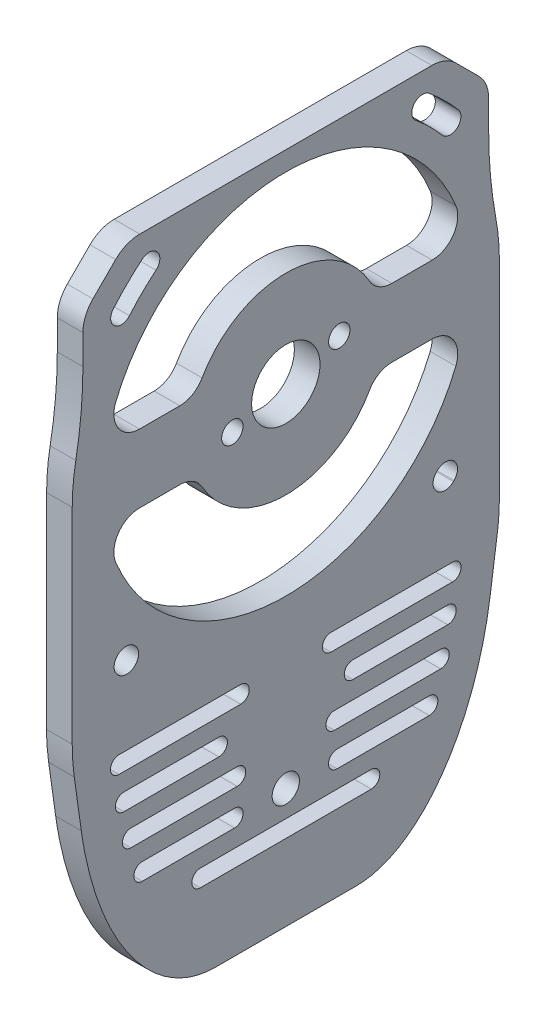
SolidWorks part; units mm, degrees
material "Thornel Mat VMA"
ref_plane "Front Plane" through (0, 0, 0) normal (0, 0, 1) x (1, 0, 0)
ref_plane "Top Plane" through (0, 0, 0) normal (0, 1, 0) x (1, 0, 0)
ref_plane "Right Plane" through (0, 0, 0) normal (1, 0, 0) x (0, 0, -1)
sketch "Sketch2" plane through (-80.1, 0, 0) normal (-1, 0, 0) x (0, 0, 1)
  line L0 (-10.1242, 29.75) -> (10.1242, 29.75)
  line L15 (23.9369, -27.3245) -> (24.7602, -21.4587)
  line L16 (25, -18.0135) -> (25, 6)
  line L17 (23.75, 19.6359) -> (23.75, 23.0931)
  line L18 (22.5784, 25.9216) -> (19.9216, 28.5784)
  line L19 (17.0931, 29.75) -> (10.1242, 29.75)
  line L20 (5.7689, 32.98) -> (1, 32.98)
  line L21 (1, 32.98) -> (1, 27.4767)
  line L22 (-1, 27.4767) -> (-1, 32.98)
  line L23 (-1, 32.98) -> (-5.7689, 32.98)
  line L24 (-10.1242, 29.75) -> (-17.0931, 29.75)
  line L25 (-19.9216, 28.5784) -> (-22.5784, 25.9216)
  line L26 (-23.75, 23.0931) -> (-23.75, 19.6359)
  line L27 (-25, 6) -> (-25, -18.0135)
  line L28 (-24.7602, -21.4587) -> (-23.9369, -27.3245)
  line L29 (-8.2627, -49) -> (8.2627, -49)
  line L30 (23.9369, -27.3245) -> (24.7602, -21.4587)
  line L31 (25, -18.0135) -> (25, 6)
  line L32 (23.75, 19.6359) -> (23.75, 23.0931)
  line L33 (22.5784, 25.9216) -> (19.9216, 28.5784)
  line L34 (17.0931, 29.75) -> (10.1242, 29.75)
  line L35 (5.7689, 32.98) -> (1, 32.98)
  line L36 (1, 32.98) -> (1, 27.4767)
  line L37 (-1, 27.4767) -> (-1, 32.98)
  line L38 (-1, 32.98) -> (-5.7689, 32.98)
  line L39 (-10.1242, 29.75) -> (-17.0931, 29.75)
  line L40 (-19.9216, 28.5784) -> (-22.5784, 25.9216)
  line L41 (-23.75, 23.0931) -> (-23.75, 19.6359)
  line L42 (-25, 6) -> (-25, -18.0135)
  line L43 (-24.7602, -21.4587) -> (-23.9369, -27.3245)
  line L44 (-8.2627, -49) -> (8.2627, -49)
  circle A0 centre (0, 6) radius 21.5
  arc A13 (25, 6) -> (24.5833, 10.5453) centre (0, 6) ccw
  arc A14 (23.75, 19.6359) -> (24.5833, 10.5453) centre (73.75, 19.6359) ccw
  arc A15 (23.75, 23.0931) -> (22.5784, 25.9216) centre (19.75, 23.0931) ccw
  arc A16 (19.9216, 28.5784) -> (17.0931, 29.75) centre (17.0931, 25.75) ccw
  arc A17 (7.207, 31.0132) -> (10.1242, 29.75) centre (10.1242, 33.75) ccw
  arc A18 (5.7689, 32.98) -> (7.207, 31.0132) centre (14.5, 37.8551) ccw
  arc A19 (-1, 27.4767) -> (1, 27.4767) centre (0, 6) ccw
  arc A20 (-7.207, 31.0132) -> (-5.7689, 32.98) centre (-14.5, 37.8551) ccw
  arc A21 (-10.1242, 29.75) -> (-7.207, 31.0132) centre (-10.1242, 33.75) ccw
  arc A22 (-17.0931, 29.75) -> (-19.9216, 28.5784) centre (-17.0931, 25.75) ccw
  arc A23 (-22.5784, 25.9216) -> (-23.75, 23.0931) centre (-19.75, 23.0931) ccw
  arc A24 (-24.5833, 10.5453) -> (-23.75, 19.6359) centre (-73.75, 19.6359) ccw
  arc A25 (-24.5833, 10.5453) -> (-25, 6) centre (0, 6) ccw
  arc A26 (25, 6) -> (24.5833, 10.5453) centre (0, 6) ccw
  arc A27 (23.75, 19.6359) -> (24.5833, 10.5453) centre (73.75, 19.6359) ccw
  arc A28 (23.75, 23.0931) -> (22.5784, 25.9216) centre (19.75, 23.0931) ccw
  arc A29 (19.9216, 28.5784) -> (17.0931, 29.75) centre (17.0931, 25.75) ccw
  arc A30 (7.207, 31.0132) -> (10.1242, 29.75) centre (10.1242, 33.75) ccw
  arc A31 (5.7689, 32.98) -> (7.207, 31.0132) centre (14.5, 37.8551) ccw
  arc A32 (-1, 27.4767) -> (1, 27.4767) centre (0, 6) ccw
  arc A33 (-7.207, 31.0132) -> (-5.7689, 32.98) centre (-14.5, 37.8551) ccw
  arc A34 (-10.1242, 29.75) -> (-7.207, 31.0132) centre (-10.1242, 33.75) ccw
  arc A35 (-17.0931, 29.75) -> (-19.9216, 28.5784) centre (-17.0931, 25.75) ccw
  arc A36 (-22.5784, 25.9216) -> (-23.75, 23.0931) centre (-19.75, 23.0931) ccw
  arc A37 (-24.5833, 10.5453) -> (-23.75, 19.6359) centre (-73.75, 19.6359) ccw
  arc A38 (-24.5833, 10.5453) -> (-25, 6) centre (0, 6) ccw
  ellipse E4 centre (10, -18.0135) end of major axis (10, -37.3575) minor radius 15 (24.7602, -21.4587) -> (25, -18.0135) ccw
  ellipse E5 centre (-10, -18.0135) end of major axis (-10, -37.3575) minor radius 15 (-25, -18.0135) -> (-24.7602, -21.4587) ccw
  ellipse E6 centre (-9.3222, -22.8431) end of major axis (-10.8998, 3.2982) minor radius 15 (-23.9369, -27.3245) -> (-8.2627, -49) ccw
  ellipse E7 centre (9.3222, -22.8431) end of major axis (7.7445, -48.9844) minor radius 15 (8.2627, -49) -> (23.9369, -27.3245) ccw
  ellipse E8 centre (10, -18.0135) end of major axis (10, -37.3575) minor radius 15 (24.7602, -21.4587) -> (25, -18.0135) ccw
  ellipse E9 centre (-10, -18.0135) end of major axis (-10, -37.3575) minor radius 15 (-25, -18.0135) -> (-24.7602, -21.4587) ccw
  ellipse E10 centre (-9.3222, -22.8431) end of major axis (-7.7445, -48.9844) minor radius 15 (-23.9369, -27.3245) -> (-8.2627, -49) ccw
  ellipse E11 centre (9.3222, -22.8431) end of major axis (7.7445, -48.9844) minor radius 15 (8.2627, -49) -> (23.9369, -27.3245) ccw
  dimension "D1" = 0
extrude "Boss-Extrude1" add sketch "Sketch2" along normal blind 3 contours L44 E11 L30 E8 L31 A26 A27 L32 A28 L33 A29 L34 L0 L36 A0 L37 L39 A35 L40 A36 L41 A37 A38 L42 E9 L43 E10 | A0 L36 L0 L37
sketch "Sketch3" plane through (-83.1, 0, 0) normal (-1, 0, 0) x (0, 0, 1)
  line L0 (0, 29.75) -> (0, -49) construction
  line L1 (17.0931, 29.75) -> (-17.0931, 29.75) construction
  line L2 (-8.2627, -49) -> (8.2627, -49) construction
  line L3 (-23.75, 23.0931) -> (-23.75, 19.6359) construction
  line L5 (18.3358, -17.75) -> (8.8925, -17.75)
  line L6 (19.2977, -17.2023) -> (19.0429, -17.4571)
  line L8 (18.3931, -19.4571) -> (19.8073, -18.0429)
  line L9 (8.8925, -19.75) -> (17.686, -19.75)
  line L10 (18.3358, -17.75) -> (8.8925, -17.75)
  line L11 (19.2977, -17.2023) -> (19.0429, -17.4571)
  line L13 (18.3931, -19.4571) -> (19.8073, -18.0429)
  line L14 (8.8925, -19.75) -> (17.686, -19.75)
  line L15 (-19.0429, -17.4571) -> (-19.2977, -17.2023)
  line L16 (-19.0429, -17.4571) -> (-19.2977, -17.2023)
  line L18 (-8.8925, -17.75) -> (-18.3358, -17.75)
  line L35 (-8.8925, -17.75) -> (-18.3358, -17.75)
  line L36 (-17.686, -19.75) -> (-8.8925, -19.75)
  line L37 (-17.686, -19.75) -> (-8.8925, -19.75)
  line L38 (-19.8073, -18.0429) -> (-18.3931, -19.4571)
  line L39 (-19.8073, -18.0429) -> (-18.3931, -19.4571)
  arc A4 (17.6468, -11.7085) -> (17.7085, -11.6468) centre (0, 6) ccw
  arc A5 (19.6918, -13.6232) -> (17.7085, -11.6468) centre (18.7002, -12.635) ccw
  arc A6 (19.6232, -13.6918) -> (19.6918, -13.6232) centre (0, 6) ccw
  arc A7 (17.6468, -11.7085) -> (19.6232, -13.6918) centre (18.635, -12.7002) ccw
  arc A8 (17.6468, -11.7085) -> (17.7085, -11.6468) centre (0, 6) ccw
  arc A9 (19.6918, -13.6232) -> (17.7085, -11.6468) centre (18.7002, -12.635) ccw
  arc A10 (19.6232, -13.6918) -> (19.6918, -13.6232) centre (0, 6) ccw
  arc A11 (17.6468, -11.7085) -> (19.6232, -13.6918) centre (18.635, -12.7002) ccw
  arc A16 (16.7926, 27.0708) -> (15.1966, 25.1465) centre (15.9946, 26.1087) ccw
  arc A17 (20.203, 23.6988) -> (16.7926, 27.0708) centre (-0.7636, 5.904) ccw
  arc A18 (18.297, 22.081) -> (20.203, 23.6988) centre (19.25, 22.8899) ccw
  arc A19 (18.297, 22.081) -> (15.1966, 25.1465) centre (-0.7636, 5.904) ccw
  arc A24 (-15.1966, 25.1465) -> (-16.7926, 27.0708) centre (-15.9946, 26.1087) ccw
  arc A25 (-15.1966, 25.1465) -> (-18.297, 22.081) centre (0.7636, 5.904) ccw
  arc A26 (-20.203, 23.6988) -> (-18.297, 22.081) centre (-19.25, 22.8899) ccw
  arc A27 (-16.7926, 27.0708) -> (-20.203, 23.6988) centre (0.7636, 5.904) ccw
  arc A28 (-19.6918, -13.6232) -> (-19.6232, -13.6918) centre (0, 6) ccw
  arc A29 (-17.7085, -11.6468) -> (-19.6918, -13.6232) centre (-18.7002, -12.635) ccw
  arc A30 (-17.7085, -11.6468) -> (-17.6468, -11.7085) centre (0, 6) ccw
  arc A31 (-19.6232, -13.6918) -> (-17.6468, -11.7085) centre (-18.635, -12.7002) ccw
  arc A32 (-19.6918, -13.6232) -> (-19.6232, -13.6918) centre (0, 6) ccw
  arc A33 (-17.7085, -11.6468) -> (-19.6918, -13.6232) centre (-18.7002, -12.635) ccw
  arc A34 (-17.7085, -11.6468) -> (-17.6468, -11.7085) centre (0, 6) ccw
  arc A35 (-19.6232, -13.6918) -> (-17.6468, -11.7085) centre (-18.635, -12.7002) ccw
  arc A38 (18.3358, -17.75) -> (19.0429, -17.4571) centre (18.3358, -16.75) ccw
  arc A39 (20.1002, -17.3358) -> (19.2977, -17.2023) centre (19.6512, -17.5559) ccw
  arc A40 (19.8073, -18.0429) -> (20.1002, -17.3358) centre (19.1002, -17.3358) ccw
  arc A41 (17.686, -19.75) -> (18.3931, -19.4571) centre (17.686, -18.75) ccw
  arc A42 (7.9787, -18.3437) -> (8.8925, -19.75) centre (8.8925, -18.75) ccw
  arc A43 (8.8925, -17.75) -> (7.9787, -18.3437) centre (8.8925, -18.75) ccw
  arc A44 (18.3358, -17.75) -> (19.0429, -17.4571) centre (18.3358, -16.75) ccw
  arc A45 (20.1002, -17.3358) -> (19.2977, -17.2023) centre (19.6512, -17.5559) ccw
  arc A46 (19.8073, -18.0429) -> (20.1002, -17.3358) centre (19.1002, -17.3358) ccw
  arc A47 (17.686, -19.75) -> (18.3931, -19.4571) centre (17.686, -18.75) ccw
  arc A48 (7.9787, -18.3437) -> (8.8925, -19.75) centre (8.8925, -18.75) ccw
  arc A49 (8.8925, -17.75) -> (7.9787, -18.3437) centre (8.8925, -18.75) ccw
  arc A50 (-19.2977, -17.2023) -> (-20.1002, -17.3358) centre (-19.6512, -17.5559) ccw
  arc A52 (-19.2977, -17.2023) -> (-20.1002, -17.3358) centre (-19.6512, -17.5559) ccw
  arc A54 (-19.0429, -17.4571) -> (-18.3358, -17.75) centre (-18.3358, -16.75) ccw
  arc A67 (-19.0429, -17.4571) -> (-18.3358, -17.75) centre (-18.3358, -16.75) ccw
  arc A69 (-7.9787, -18.3437) -> (-8.8925, -17.75) centre (-8.8925, -18.75) ccw
  arc A71 (-7.9787, -18.3437) -> (-8.8925, -17.75) centre (-8.8925, -18.75) ccw
  arc A73 (-8.8925, -19.75) -> (-7.9787, -18.3437) centre (-8.8925, -18.75) ccw
  arc A75 (-8.8925, -19.75) -> (-7.9787, -18.3437) centre (-8.8925, -18.75) ccw
  arc A77 (-18.3931, -19.4571) -> (-17.686, -19.75) centre (-17.686, -18.75) ccw
  arc A79 (-18.3931, -19.4571) -> (-17.686, -19.75) centre (-17.686, -18.75) ccw
  arc A81 (-20.1002, -17.3358) -> (-19.8073, -18.0429) centre (-19.1002, -17.3358) ccw
  arc A83 (-20.1002, -17.3358) -> (-19.8073, -18.0429) centre (-19.1002, -17.3358) ccw
  dimension "D2" = 1.25
  dimension "D7" = 3.2554
  dimension "D10" = 25
  dimension "D3" = 3.2188
  dimension "D8" = 3.6413
  dimension "D9" = 4.5
  dimension "D1" = 0
  dimension "D4" = 0
  dimension "D5" = 0
  dimension "D6" = 0
extrude "Cut-Extrude1" cut sketch "Sketch3" against normal through all contours A24 A27 A26 A25 | A32 A35 A34 A33 | A8 A11 A10 A9 | A19 A18 A17 A16
sketch "Sketch4" plane through (-80.1, 0, 0) normal (1, 0, 0) x (0, 0, -1)
  circle A0 centre (0, -35) radius 1.6
  dimension "D1" = 3.2
  dimension "D2" = 35
extrude "Cut-Extrude2" cut sketch "Sketch4" against normal through all contours A0
sketch "Sketch5" plane through (-80.1, 0, 0) normal (1, 0, 0) x (0, 0, -1)
  line L0 (-19.5212, -22.8125) -> (-5.2845, -22.8125) construction
  line L3 (-19.5212, -21.8125) -> (-5.2845, -21.8125)
  line L16 (0, -15.5) -> (0, -49) construction
  line L17 (8.2627, -49) -> (-8.2627, -49) construction
  line L18 (-19.5212, -23.8125) -> (-5.2845, -23.8125)
  line L19 (-18.9502, -26.875) -> (-7.8381, -26.875) construction
  line L20 (-18.9502, -25.875) -> (-7.8381, -25.875)
  line L21 (-18.9502, -27.875) -> (-7.8381, -27.875)
  line L22 (-16.7931, -35) -> (-6, -35) construction
  line L23 (-16.7931, -34) -> (-6, -34)
  line L24 (-16.7931, -36) -> (-6, -36)
  line L25 (-10, -39.0625) -> (10, -39.0625) construction
  line L26 (-8.2627, -45) -> (8.2627, -45)
  line L27 (19.9757, -26.7686) -> (20.799, -20.9028)
  line L28 (21, -18.0135) -> (21, 6)
  line L29 (19.75, 19.6359) -> (19.75, 23.0931)
  line L30 (19.75, 23.0931) -> (17.0931, 25.75)
  line L31 (17.0931, 25.75) -> (-17.0931, 25.75)
  line L32 (-17.0931, 25.75) -> (-19.75, 23.0931)
  line L33 (-19.75, 23.0931) -> (-19.75, 19.6359)
  line L34 (-21, 6) -> (-21, -18.0135)
  line L35 (-20.799, -20.9028) -> (-19.9757, -26.7686)
  line L36 (-8.2627, -45) -> (8.2627, -45) construction
  line L37 (19.9757, -26.7686) -> (20.799, -20.9028) construction
  line L38 (21, -18.0135) -> (21, 6) construction
  line L39 (19.75, 19.6359) -> (19.75, 23.0931) construction
  line L40 (19.75, 23.0931) -> (17.0931, 25.75) construction
  line L41 (17.0931, 25.75) -> (-17.0931, 25.75) construction
  line L42 (-17.0931, 25.75) -> (-19.75, 23.0931) construction
  line L43 (-19.75, 23.0931) -> (-19.75, 19.6359) construction
  line L44 (-21, 6) -> (-21, -18.0135) construction
  line L45 (-20.799, -20.9028) -> (-19.9757, -26.7686) construction
  line L46 (-10, -38.0625) -> (10, -38.0625)
  line L47 (-10, -40.0625) -> (10, -40.0625)
  line L48 (-18.13, -30.9375) -> (-5.6903, -30.9375) construction
  line L49 (-8.3434, -18.75) -> (-8.3434, -22.8125) construction
  line L50 (-8.3434, -22.8125) -> (-8.3434, -26.875) construction
  line L51 (-18.13, -29.9375) -> (-5.6903, -29.9375)
  line L52 (-6, -35) -> (-6, -39.0625) construction
  line L53 (19.5212, -22.8125) -> (5.2845, -22.8125) construction
  line L54 (19.5212, -21.8125) -> (5.2845, -21.8125)
  line L55 (19.5212, -23.8125) -> (5.2845, -23.8125)
  line L56 (18.9502, -26.875) -> (7.8381, -26.875) construction
  line L57 (18.9502, -25.875) -> (7.8381, -25.875)
  line L58 (18.9502, -27.875) -> (7.8381, -27.875)
  line L59 (16.7931, -35) -> (6, -35) construction
  line L60 (16.7931, -34) -> (6, -34)
  line L61 (16.7931, -36) -> (6, -36)
  line L62 (-18.13, -31.9375) -> (-5.6903, -31.9375)
  line L63 (-8.3434, -26.875) -> (-8.3434, -30.9375) construction
  line L64 (-8.3434, -30.9375) -> (-8.3434, -35) construction
  line L65 (18.13, -30.9375) -> (5.6903, -30.9375) construction
  line L66 (18.13, -29.9375) -> (5.6903, -29.9375)
  line L67 (18.13, -31.9375) -> (5.6903, -31.9375)
  circle A13 centre (0, 6) radius 21.5 construction
  arc A14 (-19.5212, -21.8125) -> (-19.5212, -23.8125) centre (-19.5212, -22.8125) ccw
  arc A15 (-5.2845, -23.8125) -> (-5.2845, -21.8125) centre (-5.2845, -22.8125) ccw
  arc A16 (-18.9502, -25.875) -> (-18.9502, -27.875) centre (-18.9502, -26.875) ccw
  arc A17 (-7.8381, -27.875) -> (-7.8381, -25.875) centre (-7.8381, -26.875) ccw
  arc A18 (-16.7931, -34) -> (-16.7931, -36) centre (-16.7931, -35) ccw
  arc A19 (-6, -36) -> (-6, -34) centre (-6, -35) ccw
  arc A20 (-10, -38.0625) -> (-10, -40.0625) centre (-10, -39.0625) ccw
  arc A21 (21, 6) -> (20.65, 9.818) centre (0, 6) ccw
  arc A22 (19.75, 19.6359) -> (20.65, 9.818) centre (73.75, 19.6359) ccw
  arc A23 (-20.65, 9.818) -> (-19.75, 19.6359) centre (-73.75, 19.6359) ccw
  arc A24 (-20.65, 9.818) -> (-21, 6) centre (0, 6) ccw
  arc A25 (21, 6) -> (20.65, 9.818) centre (0, 6) ccw construction
  arc A26 (19.75, 19.6359) -> (20.65, 9.818) centre (73.75, 19.6359) ccw construction
  arc A27 (-20.65, 9.818) -> (-19.75, 19.6359) centre (-73.75, 19.6359) ccw construction
  arc A28 (-20.65, 9.818) -> (-21, 6) centre (0, 6) ccw construction
  arc A29 (10, -40.0625) -> (10, -38.0625) centre (10, -39.0625) ccw
  circle A31 centre (0, -35) radius 1.6 construction
  arc A32 (19.5212, -21.8125) -> (19.5212, -23.8125) centre (19.5212, -22.8125) cw
  arc A33 (5.2845, -23.8125) -> (5.2845, -21.8125) centre (5.2845, -22.8125) cw
  arc A34 (18.9502, -25.875) -> (18.9502, -27.875) centre (18.9502, -26.875) cw
  arc A35 (7.8381, -27.875) -> (7.8381, -25.875) centre (7.8381, -26.875) cw
  arc A36 (16.7931, -34) -> (16.7931, -36) centre (16.7931, -35) cw
  arc A37 (6, -36) -> (6, -34) centre (6, -35) cw
  arc A38 (-18.13, -29.9375) -> (-18.13, -31.9375) centre (-18.13, -30.9375) ccw
  arc A39 (-5.6903, -31.9375) -> (-5.6903, -29.9375) centre (-5.6903, -30.9375) ccw
  arc A40 (18.13, -29.9375) -> (18.13, -31.9375) centre (18.13, -30.9375) cw
  arc A41 (5.6903, -31.9375) -> (5.6903, -29.9375) centre (5.6903, -30.9375) cw
  spline S0 degree 3 poles (-619.9963, 2887.8904) (-69.869, 105.4395) (-14.5698, -51.992) (9.9263, -44.7153) (10.157, -44.6305) (10.6027, -44.4384) (10.8189, -44.3309) (11.451, -43.9799) (11.8505, -43.7082) (12.616, -43.1069) (12.9744, -42.783) (13.9923, -41.7614) (14.5967, -41.0131) (15.7014, -39.4225) (16.1908, -38.5939) (17.0722, -36.8955) (17.4645, -36.0239) (18.1691, -34.2434) (18.4816, -33.3333) (52.0738, 79.3332) (-469.1986, 312.8033) (2990.0104, -327.4099) knots -3.201307 -3.201307 -3.201307 -3.201307 0.0625 0.0625 0.09375 0.09375 0.125 0.125 0.1875 0.1875 0.25 0.25 0.375 0.375 0.5 0.5 0.625 0.625 0.75 0.75 15.863509 15.863509 15.863509 15.863509 only from (8.2627, -45) to (19.9757, -26.7686)
  spline S1 degree 3 poles (-2973.8488, -80.8817) (4224.9302, -312.1589) (-4881.072, 590.8382) (2943.2252, 316.0456) knots -92.416825 -92.416825 -92.416825 -92.416825 186.086596 186.086596 186.086596 186.086596 only from (20.799, -20.9028) to (21, -18.0135)
  spline S2 degree 3 poles (-2943.1386, 316.0486) (4880.9792, 590.8306) (-4224.8441, -312.1521) (2973.7782, -80.884) knots -185.085569 -185.085569 -185.085569 -185.085569 93.415914 93.415914 93.415914 93.415914 only from (-21, -18.0135) to (-20.799, -20.9028)
  spline S3 degree 3 poles (-2948.5818, -561.175) (653.9359, 478.7525) (-57.9846, 99.6654) (-18.4971, -33.2848) (-18.1902, -34.1843) (-17.4936, -35.9559) (-17.1041, -36.8281) (-16.2223, -38.5388) (-15.7268, -39.3816) (-14.9002, -40.578) (-14.6102, -40.9665) (-13.9958, -41.7187) (-13.6707, -42.083) (-12.9888, -42.7697) (-12.6312, -43.0935) (-12.063, -43.542) (-11.8682, -43.6852) (-11.4663, -43.9572) (-11.2581, -44.0864) (-10.6187, -44.4433) (-10.1754, -44.64) (-9.475, -44.85) (-9.2346, -44.9057) (17.2591, -49.0088) (68.6985, 157.2813) (426.516, 2922.3676) knots -17.860511 -17.860511 -17.860511 -17.860511 0.25 0.25 0.375 0.375 0.5 0.5 0.625 0.625 0.6875 0.6875 0.75 0.75 0.8125 0.8125 0.84375 0.84375 0.875 0.875 0.9375 0.9375 0.96875 0.96875 4.368319 4.368319 4.368319 4.368319 only from (-19.9757, -26.7686) to (-8.2627, -45)
  spline S4 degree 3 poles (8.2627, -45) (8.7534, -45) (9.2294, -44.9223) (9.9263, -44.7153) (10.157, -44.6305) (10.6027, -44.4384) (10.8189, -44.3309) (11.451, -43.9799) (11.8505, -43.7082) (12.616, -43.1069) (12.9744, -42.783) (13.9923, -41.7614) (14.5967, -41.0131) (15.7014, -39.4225) (16.1908, -38.5939) (17.0722, -36.8955) (17.4645, -36.0239) (18.1691, -34.2434) (18.4816, -33.3333) (19.3082, -30.5608) (19.7076, -28.6791) (19.9757, -26.7686) knots 0 0 0 0 0.0625 0.0625 0.09375 0.09375 0.125 0.125 0.1875 0.1875 0.25 0.25 0.375 0.375 0.5 0.5 0.625 0.625 0.75 0.75 1 1 1 1 construction
  spline S5 degree 3 poles (20.799, -20.9028) (20.9335, -19.9444) (21, -18.9813) (21, -18.0135) knots 0 0 0 0 1 1 1 1 construction
  spline S6 degree 3 poles (-21, -18.0135) (-21, -18.9813) (-20.9335, -19.9444) (-20.799, -20.9028) knots 0 0 0 0 1 1 1 1 construction
  spline S7 degree 3 poles (-19.9757, -26.7686) (-19.7073, -28.681) (-19.3091, -30.5508) (-18.4971, -33.2848) (-18.1902, -34.1843) (-17.4936, -35.9559) (-17.1041, -36.8281) (-16.2223, -38.5388) (-15.7268, -39.3816) (-14.9002, -40.578) (-14.6102, -40.9665) (-13.9958, -41.7187) (-13.6707, -42.083) (-12.9888, -42.7697) (-12.6312, -43.0935) (-12.063, -43.542) (-11.8682, -43.6852) (-11.4663, -43.9572) (-11.2581, -44.0864) (-10.6187, -44.4433) (-10.1754, -44.64) (-9.475, -44.85) (-9.2346, -44.9057) (-8.752, -44.9804) (-8.5085, -45) (-8.2627, -45) knots 0 0 0 0 0.25 0.25 0.375 0.375 0.5 0.5 0.625 0.625 0.6875 0.6875 0.75 0.75 0.8125 0.8125 0.84375 0.84375 0.875 0.875 0.9375 0.9375 0.96875 0.96875 1 1 1 1 construction
  point P2 (-12.4028, -22.8125)
  point P7 (-13.3942, -26.875)
  point P14 (-11.3966, -35)
  point P28 (0, -39.0625)
  point P42 (-11.9101, -30.9375)
  point P51 (12.4028, -22.8125)
  point P63 (13.3942, -26.875)
  point P70 (11.3966, -35)
  point P77 (0, -35)
  point P89 (11.9101, -30.9375)
  dimension "D2" = 6
  dimension "D3" = 10
  dimension "D4" = 1
  dimension "D5" = 18.75
  dimension "D1" = 4
extrude "Cut-Extrude3" cut sketch "Sketch5" against normal through all
sketch "Sketch6" plane through (-83.1, 0, 0) normal (-1, 0, 0) x (0, 0, 1)
  line L1 (21.5, 2) -> (-21.5, 2)
  line L2 (21.5, 2) -> (21.5, 10)
  line L3 (21.5, 10) -> (-21.5, 10)
  line L4 (-21.5, 2) -> (-21.5, 10)
  line L5 (21.5, 2) -> (-21.5, 10) construction
  line L6 (21.5, 10) -> (-21.5, 2) construction
  circle A0 centre (0, 6) radius 21.5 construction
  circle A1 centre (0, 6) radius 11.25
  arc A2 (5.4542, 5.1995) -> (7.0612, 3.2844) centre (6.2577, 4.2419) ccw construction
  arc A3 (7.0612, 3.2844) -> (5.4542, 5.1995) centre (6.2577, 4.2419) ccw construction
  arc A4 (-7.0612, 8.7156) -> (-5.4542, 6.8005) centre (-6.2577, 7.7581) ccw construction
  arc A5 (-5.4542, 6.8005) -> (-7.0612, 8.7156) centre (-6.2577, 7.7581) ccw construction
  arc A6 (5.4542, 5.1995) -> (7.0612, 3.2844) centre (6.2577, 4.2419) ccw
  arc A7 (7.0612, 3.2844) -> (5.4542, 5.1995) centre (6.2577, 4.2419) ccw
  arc A8 (-7.0612, 8.7156) -> (-5.4542, 6.8005) centre (-6.2577, 7.7581) ccw
  arc A9 (-5.4542, 6.8005) -> (-7.0612, 8.7156) centre (-6.2577, 7.7581) ccw
  point P0 (0, 6)
  dimension "D2" = 22.5
  dimension "D1" = 8
extrude "Boss-Extrude3" add sketch "Sketch6" against normal up to surface (3 mm away) contours A1 L3 L4 L1 | L3 A1 L1 A9 A8 A7 A6 | L3 A1 | L1 A1 | A1 L1 L2 L3 up to face at (-80.1, -30.9375, 11.9101)
fillet "Fillet1" radius 3 8 edges at (-81.6, 2, 10.5149) (-81.6, 2, -10.5149) (-81.6, 2, 21.1246) (-81.6, 2, -21.1246) (-81.6, 10, 10.5149) (-81.6, 10, -10.5149) (-81.6, 10, 21.1246) (-81.6, 10, -21.1246)
sketch "Sketch7" plane through (-80.1, 0, 0) normal (1, 0, 0) x (0, 0, -1)
  circle A0 centre (0, 6) radius 4
  arc A1 (9.7991, 11.5263) -> (-9.7991, 11.5263) centre (0, 6) ccw construction
  dimension "D1" = 8
extrude "Cut-Extrude4" cut sketch "Sketch7" against normal through all
